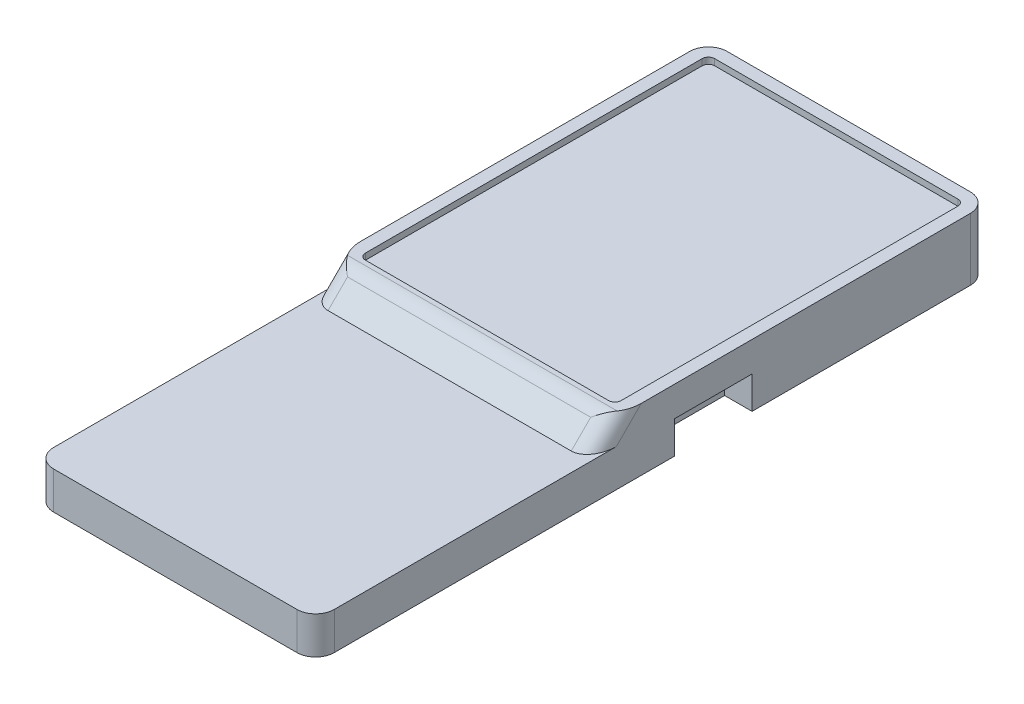
SolidWorks part; units mm, degrees
ref_plane "Спереди" through (0, 0, 0) normal (0, 0, 1) x (1, 0, 0)
ref_plane "Сверху" through (0, 0, 0) normal (0, 1, 0) x (1, 0, 0)
ref_plane "Справа" through (0, 0, 0) normal (1, 0, 0) x (0, 0, -1)
sketch "surface_sketch" plane through (0, 0, 0) normal (0, 1, 0) x (1, 0, 0)
  line L2 (-12.4, -15) -> (10.1, -15)
  line L3 (10.1, -15) -> (10.1, 15)
  line L4 (0.1, 0) -> (0.1, -15) construction
  line L5 (0.1, 0) -> (10.1, 0) construction
  line L7 (-12.4, 15) -> (10.1, 15)
  line L8 (-12.4, 15) -> (-12.4, -15)
  line L9 (-3.65, -15) -> (-3.65, -7.5) construction
  line L10 (-3.65, -7.5) -> (0.1, -7.5) construction
  line L11 (-3.65, -7.5) -> (-3.65, 0) construction
  line L12 (-3.65, 0) -> (-3.65, 7.5) construction
  line L13 (-1.3, 7.5) -> (-6, 7.5)
  line L14 (-6, 0) -> (-1.3, 0)
  line L15 (-6, -7.5) -> (-1.3, -7.5)
  line L16 (6.2, -7.5) -> (1.5, -7.5)
  line L17 (6.2, 0) -> (1.5, 0) construction
  line L18 (3.85, 7.5) -> (1.5, 7.5)
  line L19 (0, 0) -> (0.1, 0) construction
  line L20 (3.85, 7.5) -> (6.2, 7.5)
  circle A0 centre (-3.65, 7.5) radius 2.35
  circle A1 centre (-3.65, 0) radius 2.35
  circle A2 centre (-3.65, -7.5) radius 2.35
  circle A3 centre (3.85, -7.5) radius 2.35
  circle A4 centre (3.85, 0) radius 2.35
  circle A5 centre (3.85, 7.5) radius 2.35
  dimension "D1" = 22.5
  dimension "D9" = 4.7
  dimension "D10" = 4.7
  dimension "D11" = 4.7
  dimension "D2" = 30
  dimension "D5" = 7.5
  dimension "D6" = 3.75
  dimension "D7" = 7.5
  dimension "D8" = 7.5
  dimension "D3" = 10
  dimension "D4" = 0.1
extrude "body" add sketch "surface_sketch" against normal blind 4.5
ref_plane "midplane" through (-1.15, 0, 0) normal (1, 0, 0) x (0, 0, -1)
sketch "Эскиз19" plane through (0, -4.5, 0) normal (0, 1, 0) x (1, 0, 0)
  line L1 (-12.4, -15) -> (10.1, -15)
  line L2 (-12.4, -15) -> (-12.4, -39)
  line L3 (-12.4, -39) -> (10.1, -39)
  line L4 (10.1, -15) -> (10.1, -39)
  dimension "D1" = 22.5
  dimension "D2" = 24
extrude "Бобышка-Вытянуть4" add sketch "Эскиз19" along normal blind 3
fillet "Скругление6" radius 1.5 4 edges at (10.1, -3, 39) (-12.4, -3, 39) (10.1, -2.25, -15) (-12.4, -2.25, -15)
sketch "magnet_cutout_sketch" plane through (0, -4.5, 0) normal (0, -1, 0) x (1, 0, 0)
  line L0 (10.1, 37.5) -> (10.1, -13.5) construction
  line L1 (7.9, 10.2) -> (10.1, 10.2)
  line L2 (7.9, 10.2) -> (7.9, 4)
  line L3 (7.9, 4) -> (10.1, 4)
  line L4 (10.1, 10.2) -> (10.1, 4)
  line L5 (9, 4) -> (9, 10.2) construction
  line L6 (7.9, 7.1) -> (10.1, 7.1) construction
  line L9 (7.9, 4) -> (7.9, -15) construction
  line L10 (-10.9, -15) -> (8.6, -15) construction
  point P0 (9, 7.1)
  dimension "D1" = 2.2
  dimension "D2" = 6.2
  dimension "D3" = 19
extrude "magnet_cutout" cut sketch "magnet_cutout_sketch" against normal blind 2.6
mirror "magnet_cutout_mirror" about plane through (-1.15, 0, 0) normal (1, 0, 0) of "magnet_cutout"
sketch "border_sketch" plane through (0, 0, 0) normal (0, 1, 0) x (1, 0, 0)
  line L0 (-12.4, -15) -> (-12.4, 13.5)
  line L1 (10.1, -15) -> (10.1, 13.5)
  line L2 (8.6, 15) -> (-10.9, 15)
  line L4 (-1.15, 15) -> (-1.15, -15.5) construction
  line L5 (-12.4, -0.75) -> (10.1, -0.75) construction
  line L6 (-10.9, 15) -> (8.6, 15) construction
  line L7 (10.1, -15) -> (10.1, 13.5) construction
  arc A2 (10.1, 13.5) -> (8.6, 15) centre (8.6, 13.5) ccw
  arc A3 (-12.4, 13.5) -> (-10.9, 15) centre (-10.9, 13.5) cw
  dimension "D1" = 1.5
extrude "border" add sketch "border_sketch" along normal blind 0.5 thin contours L0 A3 L2 A2 L1
sketch "Эскиз21" plane through (-12.4, 0, 0) normal (-1, 0, 0) x (0, 0, 1)
  line L0 (15, 0.5) -> (17, -1.5)
  line L1 (15, -1.5) -> (37.5, -1.5) construction
  line L2 (17, -1.5) -> (15, -1.5)
  line L3 (15, -1.5) -> (14, -1.5)
  line L4 (14, -1.5) -> (14, 0.5)
  line L5 (15, 0.5) -> (-13.5, 0.5) construction
  line L6 (14, 0.5) -> (15, 0.5)
  line L7 (15, 0.5) -> (15, -1.5) construction
  dimension "D1" = 1
extrude "champfer" add sketch "Эскиз21" against normal up to surface (22.5 mm away) up to face at (10.1, -2.38, 10.64)
fillet "Скругление7" radius 1.5 2 edges at (10.1, -0.5, 16) (-12.4, -0.5, 16)
fillet "Скругление8" radius 0.5 2 edges at (-11.4, 0.25, 14) (9.1, 0.25, 14)
sketch "Эскиз22" plane through (-12.4, 0, 0) normal (-1, 0, 0) x (0, 0, 1)
  line L0 (12.8787, 0.5) -> (14.3787, 0.5)
  line L1 (15.4393, 0.0607) -> (17, -1.5)
  line L2 (17, -1.5) -> (17.9233, -1.5)
  line L3 (14.8787, -1.5) -> (37.5, -1.5) construction
  line L4 (17.9233, -1.5) -> (15.1812, 1.2421)
  line L5 (15.1812, 1.2421) -> (12.8787, 1.1224)
  line L6 (12.8787, 1.1224) -> (12.8787, 0.5)
  arc A0 (15.4393, 0.0607) -> (14.3787, 0.5) centre (14.3787, -1) ccw
  point P13 (15, 0.5)
  dimension "D1" = 1.5
extrude "Вырез-Вытянуть1" cut sketch "Эскиз22" against normal through all
equation "\"hole_diam\"= 4.7мм"
equation "\"cell_width\"= \"cell_pace\""
equation "\"cell_pace\"= 22.5мм'distance between neighbouring cells"
equation "\"holes_horisontal_dist\"= 7.5"
equation "\"holes_vertical_dist\"= \"holes_horisontal_dist\""
equation "\"cell_length\"= \"holes_vertical_dist\" * 4"
equation "\"char_width\"= 15"
equation "\"char_thickness\"= 2.5"
equation "\"char_height\"= 22"
equation "\"D1@body\" = \"cell_surface_height\""
equation "\"char_champfer_width\"= 1"
equation "\"char_depth\"= 1.5"
equation "\"D1@Эскиз19\"=\"cell_width\""
equation "\"D2@surface_sketch\"=\"cell_length\""
equation "\"D9@surface_sketch\"=\"hole_diam\""
equation "\"D8@surface_sketch\"=\"holes_vertical_dist\""
equation "\"D6@surface_sketch\"=\"holes_horisontal_dist\"/2"
equation "\"D1@surface_sketch\"=\"cell_width\""
equation "\"D5@surface_sketch\"=\"holes_vertical_dist\""
equation "\"D7@surface_sketch\"=\"holes_vertical_dist\""
equation "\"magnet_cut_height\"= 2.6"
equation "\"magnet_cut_width\"= 6.2"
equation "\"magnet_cut_depth\"= 2.2"
equation "\"D1@magnet_cutout_sketch\" = \"magnet_cut_depth\""
equation "\"D2@magnet_cutout_sketch\" = \"magnet_cut_width\""
equation "\"D1@magnet_cutout\" = \"magnet_cut_height\""
equation "\"border_width\"= 1"
equation "\"border_height\"= 0.5"
equation "\"D1\"= \"border_height\""
equation "\"D5@border\" = \"border_width\""
equation "\"D2@back_complementary_holes_sketch\" = \"hole_diam\" - 0.2"
equation "\"D3@back_complementary_holes_sketch\" = \"holes_vertical_dist\""
equation "\"D4@back_complementary_holes_sketch\" = \"holes_horisontal_dist\" / 2"
equation "\"D5@back_complementary_holes_sketch\" = \"holes_vertical_dist\""
equation "\"D6@back_complementary_holes_sketch\" = \"holes_vertical_dist\""
equation "\"D7@back_complementary_holes_sketch\" = \"hole_diam\" - 0.2"
equation "\"D8@back_complementary_holes_sketch\" = \"hole_diam\" - 0.2"
